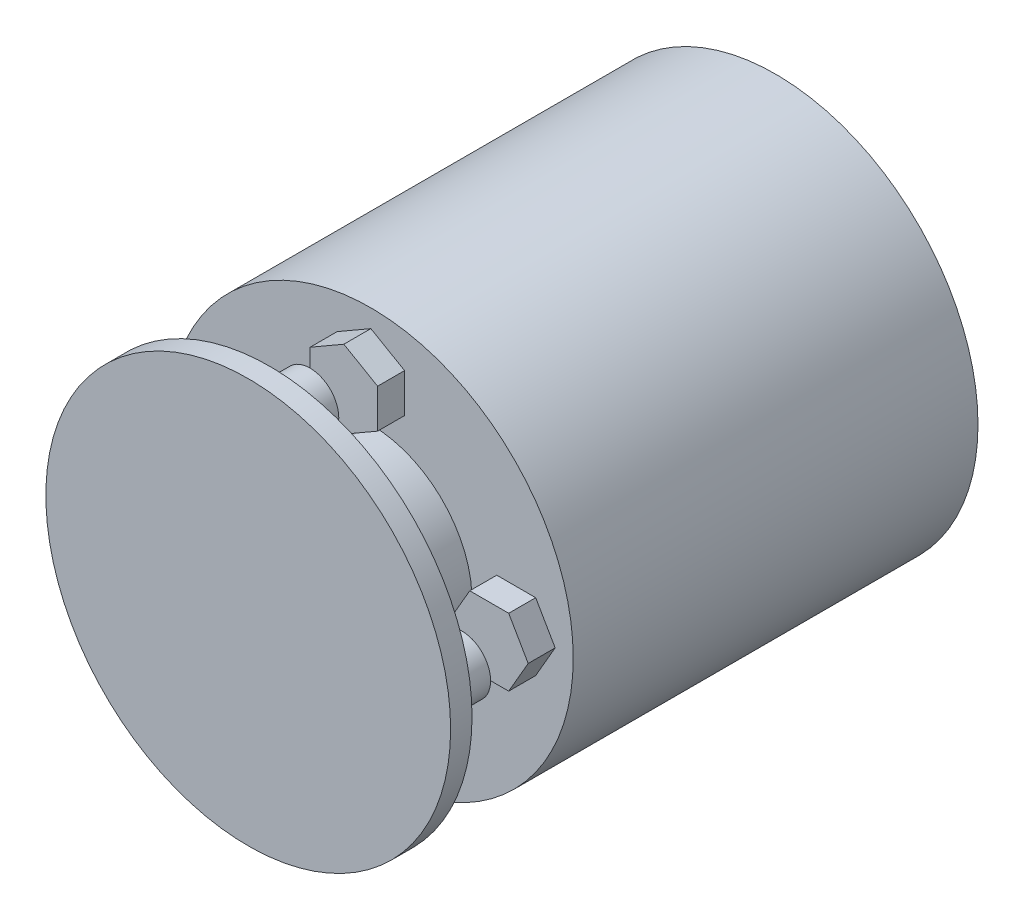
SolidWorks part; units mm, degrees
ref_plane "Front Plane" through (0, 0, 0) normal (0, 0, 1) x (1, 0, 0)
ref_plane "Top Plane" through (0, 0, 0) normal (0, 1, 0) x (1, 0, 0)
ref_plane "Right Plane" through (0, 0, 0) normal (1, 0, 0) x (0, 0, -1)
sketch "Sketch1" plane through (0, 0, 0) normal (0, 0, 1) x (1, 0, 0)
  line L0 (-2, 7.5) -> (2, 7.5)
  line L1 (0, 15.7745) -> (5, 18.6612)
  line L2 (5, 18.6612) -> (5, 24.4348)
  line L3 (5, 24.4348) -> (0, 27.3215)
  line L4 (0, 27.3215) -> (-5, 24.4348)
  line L5 (-5, 24.4348) -> (-5, 18.6612)
  line L6 (-5, 18.6612) -> (0, 15.7745)
  line L7 (2, 7.5) -> (2, 5.6569)
  line L8 (-2, 7.5) -> (-2, 5.6569)
  line L9 (-7.8123, 14.1512) -> (-2.8123, 14.1512)
  line L10 (-2.8123, 14.1512) -> (-2.8123, 15.4012)
  line L11 (-2.8123, 15.4012) -> (0.1877, 15.4012)
  line L12 (0.1877, 15.4012) -> (0.1877, 9.9012)
  line L13 (0.1877, 9.9012) -> (-2.8123, 9.9012)
  line L14 (-2.8123, 9.9012) -> (-2.8123, 11.1512)
  line L15 (-2.8123, 11.1512) -> (-7.8123, 11.1512)
  line L16 (-7.8123, 11.1512) -> (-7.8123, 14.1512)
  circle A0 centre (0, 0) radius 21.548 construction
  circle A1 centre (0, 21.548) radius 5 construction
  arc A2 (-2, 5.6569) -> (2, 5.6569) centre (0, 0) ccw
  point P14 (0, 7.5)
  point P17 (0, -6)
  point P25 (-9.8813, 9.3581)
  point P26 (-4.0792, 7.5)
  point P27 (0.1877, 9.9012)
  dimension "D1" = 43.096
  dimension "D3" = 12
  dimension "D4" = 4
  dimension "D2" = 10
  dimension "D5" = 13.5
  dimension "D6" = 3
  dimension "D7" = 3
  dimension "D8" = 5.5
  dimension "D9" = 5
sketch "Sketch2" plane through (0, 0, 0) normal (1, 0, 0) x (0, 0, -1)
  line L0 (-1885.7899, 0) -> (92403.7069, 0) construction
  line L1 (0, 0) -> (0, 30)
  line L2 (0, 30) -> (-60, 30)
  line L3 (-60, 30) -> (-60, 6)
  line L4 (-60, 6) -> (-75, 6)
  line L5 (-75, 6) -> (-75, 30)
  line L6 (-75, 30) -> (-78.175, 30)
  line L7 (-78.175, 30) -> (-78.175, 0)
  line L8 (-78.175, 0) -> (0, 0)
  dimension "D1" = 60
  dimension "D2" = 12
  dimension "D3" = 15
  dimension "D4" = 60
  dimension "D5" = 3.175
revolve "Revolve1" add sketch "Sketch2" angle 360 about L0
sketch "Sketch3" plane through (0, 0, 60) normal (0, 0, 1) x (1, 0, 0)
  line L0 (15.7745, 0) -> (18.6612, -5)
  line L1 (0, 15.7745) -> (5, 18.6612)
  line L2 (5, 18.6612) -> (5, 24.4348)
  line L3 (5, 24.4348) -> (0, 27.3215)
  line L4 (0, 27.3215) -> (-5, 24.4348)
  line L5 (-5, 24.4348) -> (-5, 18.6612)
  line L6 (-5, 18.6612) -> (0, 15.7745)
  line L7 (18.6612, -5) -> (24.4348, -5)
  line L8 (24.4348, -5) -> (27.3215, 0)
  line L9 (27.3215, 0) -> (24.4348, 5)
  line L10 (24.4348, 5) -> (18.6612, 5)
  line L11 (18.6612, 5) -> (15.7745, 0)
  line L12 (0, -15.7745) -> (-5, -18.6612)
  line L13 (-5, -18.6612) -> (-5, -24.4348)
  line L14 (-5, -24.4348) -> (0, -27.3215)
  line L15 (0, -27.3215) -> (5, -24.4348)
  line L16 (5, -24.4348) -> (5, -18.6612)
  line L17 (5, -18.6612) -> (0, -15.7745)
  line L18 (-15.7745, 0) -> (-18.6612, 5)
  line L19 (-18.6612, 5) -> (-24.4348, 5)
  line L20 (-24.4348, 5) -> (-27.3215, 0)
  line L21 (-27.3215, 0) -> (-24.4348, -5)
  line L22 (-24.4348, -5) -> (-18.6612, -5)
  line L23 (-18.6612, -5) -> (-15.7745, 0)
  line L24 (0, -15.7745) -> (0, -27.3215) construction
  circle A0 centre (0, 21.548) radius 5 construction
  point P1 (0, -21.548)
  point P9 (0, 0)
  point P10 (-3.5964, 16.8464)
  point P29 (0, 0)
  point P30 (0, 0)
  dimension "D1" = 10
  dimension "D3" = 43.096
  dimension "D2" = 4
extrude "Boss-Extrude1" add sketch "Sketch3" along normal blind 4
sketch "Sketch4" plane through (0, 0, 75) normal (0, 0, -1) x (-1, 0, 0)
  circle A0 centre (0, 22.5) radius 4.25
  circle A1 centre (22.5, 0) radius 4.25
  circle A2 centre (0, -22.5) radius 4.25
  circle A3 centre (-22.5, 0) radius 4.25
  point P2 (20.7061, -2.5224)
  point P3 (0, 0)
  point P4 (-3.9906, 17.2802)
  point P11 (0, 0)
  point P12 (0, 0)
  dimension "D1" = 4
  dimension "D3" = 8.5
  dimension "D2" = 45
extrude "Boss-Extrude2" add sketch "Sketch4" along normal blind 6
sketch "Sketch5" plane through (0, 0, 60) normal (0, 0, 1) x (1, 0, 0)
  line L8 (-2, 5.6569) -> (-2, 8)
  line L9 (-2, 8) -> (2, 8)
  line L10 (2, 8) -> (2, 5.6569)
  circle A1 centre (0, 0) radius 15
  arc A2 (-2, 5.6569) -> (2, 5.6569) centre (0, 0) ccw
  point P8 (0, 8)
  dimension "D1" = 30
  dimension "D2" = 12
  dimension "D3" = 4
  dimension "D4" = 8
extrude "Boss-Extrude3" add sketch "Sketch5" along normal blind 15 separate body
ref_plane "Plane2" through (0, 0, 67.5) normal (0, 0, 1) x (1, 0, 0)
sketch "Sketch7" plane through (0, 0, 67.5) normal (0, 0, 1) x (1, 0, 0)
  line L0 (12.8428, -10.5) -> (12.8428, -7.75)
  line L1 (12.8428, -7.75) -> (2, -7.75)
  line L2 (2, -7.75) -> (2, -9)
  line L3 (2, -9) -> (-4, -9)
  line L8 (0, -6) -> (0, -15) construction
  line L9 (-1000, -10.5) -> (49000, -10.5) construction
  line L10 (-4, -9) -> (-4, -10.5)
  line L11 (-4, -10.5) -> (12.8428, -10.5)
  arc A0 (-2, 5.6569) -> (2, 5.6569) centre (0, 0) ccw construction
  circle A1 centre (0, 0) radius 15 construction
  point P5 (0, -10.5)
  point P7 (0, 0)
  dimension "D1" = 5.5
  dimension "D2" = 3
  dimension "D3" = 2
  dimension "D4" = 6
revolve "Cut-Revolve3" cut sketch "Sketch7" angle 360 about L9
sketch "Sketch9" plane through (-4, 0, 0) normal (1, 0, 0) x (0, 0, -1)
  line L1 (-65.9123, -13.25) -> (-64.3246, -10.5)
  line L2 (-64.3246, -10.5) -> (-65.9123, -7.75)
  line L3 (-65.9123, -7.75) -> (-69.0877, -7.75)
  line L4 (-69.0877, -7.75) -> (-70.6754, -10.5)
  line L5 (-70.6754, -10.5) -> (-69.0877, -13.25)
  line L6 (-69.0877, -13.25) -> (-65.9123, -13.25)
  circle A0 centre (-67.5, -10.5) radius 2.75 construction
  dimension "D1" = 5.5
extrude "Cut-Extrude1" cut sketch "Sketch9" against normal through all and the other way blind 2
split "Split1" trim tools "Right Plane" bodies to split 106 resulting bodies 107 108
sketch "Sketch10" plane through (0, 0, 0) normal (-1, 0, 0) x (0, 0, 1)
  line L0 (67.5, -33) -> (67.5, 33) construction
  line L1 (69.5, 13.5) -> (65.5, 13.5)
  line L2 (69.5, 13.5) -> (69.5, 9.5)
  line L3 (69.5, 9.5) -> (65.5, 9.5)
  line L4 (65.5, 13.5) -> (65.5, 9.5)
  line L5 (69.5, 13.5) -> (65.5, 9.5) construction
  line L6 (69.5, 9.5) -> (65.5, 13.5) construction
  line L7 (60, 8) -> (60, 15) construction
  point P0 (67.5, 11.5)
  point P9 (60, 11.5)
  dimension "D1" = 4
  dimension "D2" = 4
extrude "Boss-Extrude4" add sketch "Sketch10" along normal blind 3
sketch "Sketch11" plane through (0, 0, 0) normal (1, 0, 0) x (0, 0, -1)
  line L0 (-69.5, 13.5) -> (-65.5, 9.5) construction
  line L1 (-69.5, 9.5) -> (-65.5, 9.5)
  line L2 (-69.5, 9.5) -> (-69.5, 13.5)
  line L3 (-69.5, 13.5) -> (-65.5, 13.5)
  line L4 (-65.5, 9.5) -> (-65.5, 13.5)
  line L5 (-75, 8) -> (-75, 15) construction
  line L6 (-67.5, 33) -> (-67.5, -33) construction
  point P6 (-75, 11.5)
  point P7 (-67.5, 11.5)
  point P8 (-70.2977, 13.5)
  dimension "D1" = 4
extrude "Cut-Extrude2" cut sketch "Sketch11" against normal blind 3
